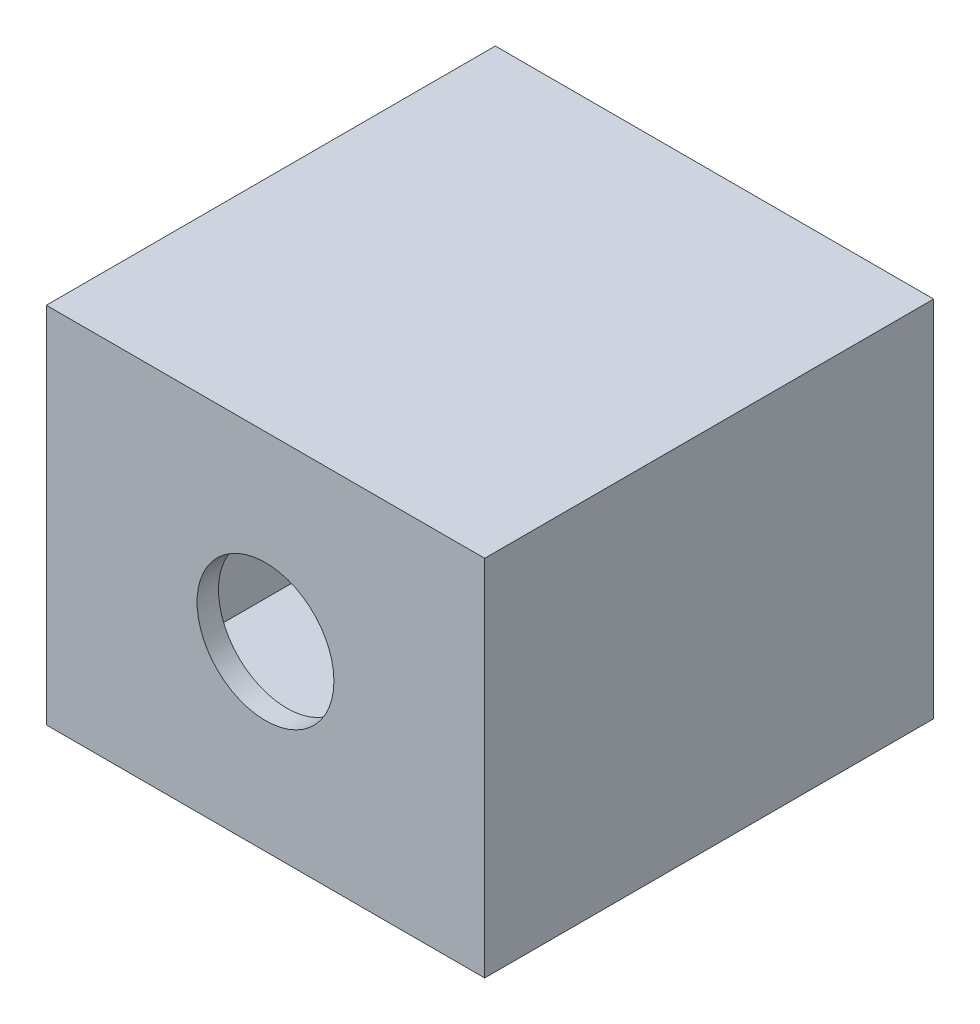
SolidWorks part; units mm, degrees
ref_plane "Alzado" through (0, 0, 0) normal (0, 0, 1) x (1, 0, 0)
ref_plane "Planta" through (0, 0, 0) normal (0, 1, 0) x (1, 0, 0)
ref_plane "Vista lateral" through (0, 0, 0) normal (1, 0, 0) x (0, 0, -1)
sketch "Croquis1" plane through (0, 0, 0) normal (0, 0, 1) x (1, 0, 0)
  line L1 (-49.0512, 11.5346) -> (-30.5512, 11.5346)
  line L2 (-49.0512, 11.5346) -> (-49.0512, -3.4654)
  line L3 (-49.0512, -3.4654) -> (-30.5512, -3.4654)
  line L4 (-30.5512, 11.5346) -> (-30.5512, -3.4654)
  line L5 (-50.0512, 12.5346) -> (-29.5512, 12.5346)
  line L6 (-50.0512, 12.5346) -> (-50.0512, -4.4654)
  line L7 (-50.0512, -4.4654) -> (-29.5512, -4.4654)
  line L8 (-29.5512, 12.5346) -> (-29.5512, -4.4654)
  dimension "D1" = 15
  dimension "D2" = 18.5
  dimension "D3" = 1
  dimension "D4" = 1
  dimension "D5" = 1
  dimension "D6" = 1
extrude "Saliente-Extruir1" add sketch "Croquis1" along normal blind 20
sketch "Croquis2" plane through (0, 0, 20) normal (0, 0, 1) x (1, 0, 0)
  line L0 (-50.0512, -4.4654) -> (-29.5512, 12.5346) construction
  line L1 (-50.0512, 12.5346) -> (-29.5512, 12.5346)
  line L2 (-50.0512, 12.5346) -> (-50.0512, -4.4654)
  line L3 (-50.0512, -4.4654) -> (-29.5512, -4.4654)
  line L4 (-29.5512, 12.5346) -> (-29.5512, -4.4654)
  line L5 (-29.5512, -4.4654) -> (-50.0512, 12.5346) construction
  circle A0 centre (-39.8012, 4.0346) radius 3.2
extrude "Saliente-Extruir2" add sketch "Croquis2" along normal blind 1
